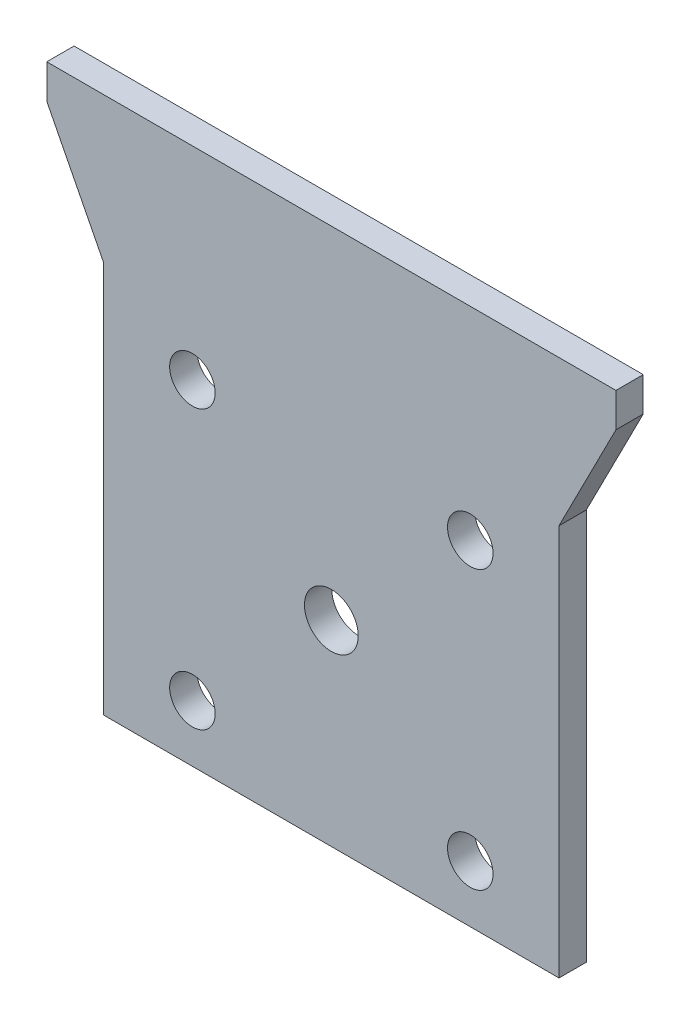
SolidWorks part; units mm, degrees
ref_plane "Front Plane" through (0, 0, 0) normal (0, 0, 1) x (1, 0, 0)
ref_plane "Top Plane" through (0, 0, 0) normal (0, 1, 0) x (1, 0, 0)
ref_plane "Right Plane" through (0, 0, 0) normal (1, 0, 0) x (0, 0, -1)
sketch "Sketch1" plane through (0, 0, 0) normal (0, 0, 1) x (1, 0, 0)
  line L0 (-25.4, 38.1) -> (-25.4, -21.85) construction
  line L1 (-25.4, -21.85) -> (25.4, -21.85)
  line L2 (25.4, -21.85) -> (25.4, 38.1) construction
  line L3 (25.4, 38.1) -> (-25.4, 38.1) construction
  line L4 (0, 38.1) -> (0, -21.85) construction
  line L5 (-25.4, -21.85) -> (-25.4, 21.85)
  line L6 (-25.4, 21.85) -> (-31.75, 34.29)
  line L7 (15.5, 15.5) -> (-15.5, 15.5) construction
  line L8 (15.5, 15.5) -> (15.5, -15.5) construction
  line L9 (15.5, -15.5) -> (-15.5, -15.5) construction
  line L10 (-15.5, 15.5) -> (-15.5, -15.5) construction
  line L11 (15.5, 15.5) -> (-15.5, -15.5) construction
  line L12 (15.5, -15.5) -> (-15.5, 15.5) construction
  line L13 (-31.75, 34.29) -> (-31.75, 38.1)
  line L14 (-31.75, 38.1) -> (31.75, 38.1)
  line L15 (31.75, 34.29) -> (31.75, 38.1)
  line L16 (25.4, 21.85) -> (31.75, 34.29)
  line L17 (25.4, -21.85) -> (25.4, 21.85)
  circle A0 centre (-15.5, 15.5) radius 2.54
  circle A1 centre (15.5, 15.5) radius 2.54
  circle A2 centre (15.5, -15.5) radius 2.54
  circle A3 centre (-15.5, -15.5) radius 2.54
  circle A4 centre (0, 0) radius 3
  point P0 (0, 0)
  point P6 (0, 0)
  dimension "D1" = 5.08
  dimension "D6" = 6
  dimension "D2" = 31
  dimension "D3" = 50.8
  dimension "D4" = 6.35
  dimension "D5" = 38.1
  dimension "D7" = 3.81
  dimension "D8" = 31.75
  dimension "D9" = 6.35
extrude "Boss-Extrude1" add sketch "Sketch1" along normal blind 3.048
